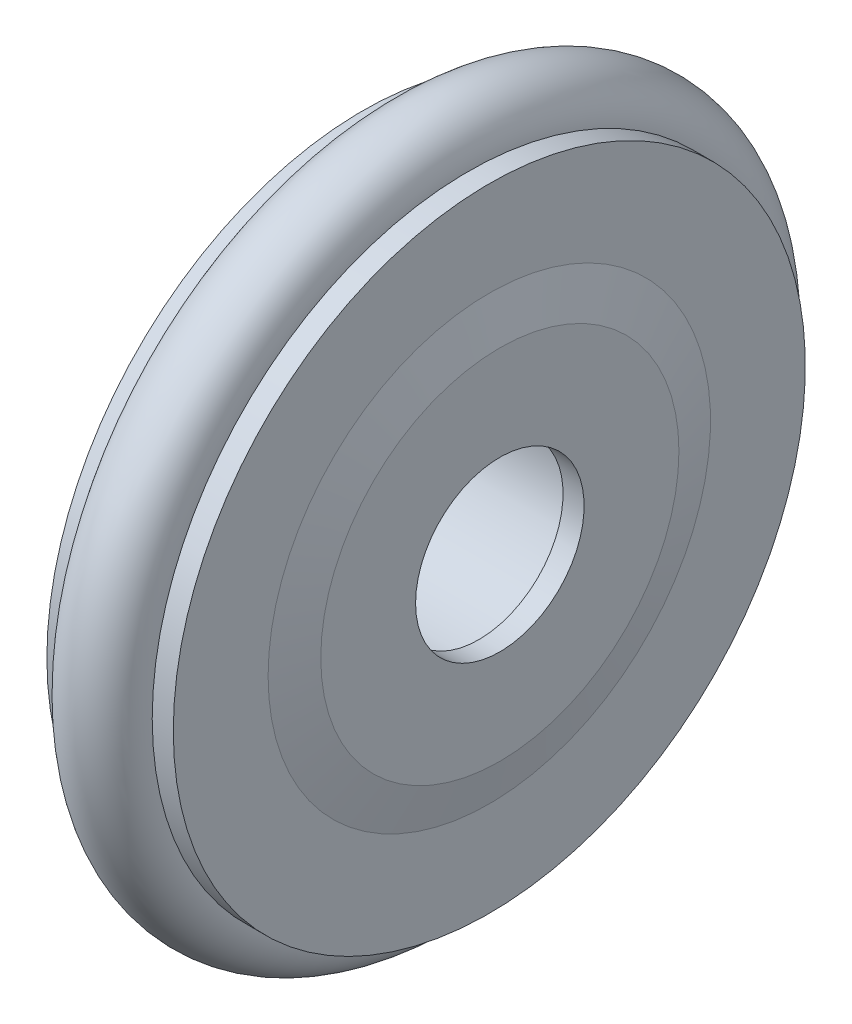
SolidWorks part; units mm, degrees
ref_plane "前视基准面" through (0, 0, 0) normal (0, 0, 1) x (1, 0, 0)
ref_plane "上视基准面" through (0, 0, 0) normal (0, 1, 0) x (1, 0, 0)
ref_plane "右视基准面" through (0, 0, 0) normal (1, 0, 0) x (0, 0, -1)
sketch "草图1" plane through (0, 0, 0) normal (0, 0, 1) x (1, 0, 0)
  line L0 (5.5, 5.1) -> (5.5, 4)
  line L1 (6.5, 8.5) -> (6.5, 4)
  line L2 (5.5, 4) -> (6.5, 4)
  line L3 (0, 15) -> (1, 15)
  line L4 (6, 10.5) -> (6.5, 8.5)
  line L5 (5, 15) -> (6, 15)
  line L6 (6, 15) -> (6, 10.5)
  line L7 (0, 0) -> (9.4205, 0) construction
  line L8 (5.5, 5.1) -> (0, 5.1)
  line L9 (0, 15) -> (0, 5.1)
  arc A0 (1, 15) -> (5, 15) centre (3, 15) ccw
  circle A1 centre (3, 15) radius 1.95
  dimension "D2" = 6
  dimension "D8" = 2
  dimension "D9" = 4.5
  dimension "D12" = 4
  dimension "D7" = 6
  dimension "D5" = 15
  dimension "D1" = 5.5
  dimension "D3" = 4
  dimension "D13" = 3.9
  dimension "D4" = 5.1
  dimension "D6" = 6.5
  dimension "D10" = 4.5
  dimension "D11" = 1
revolve "旋转1" add sketch "草图1" angle 360 about L7
